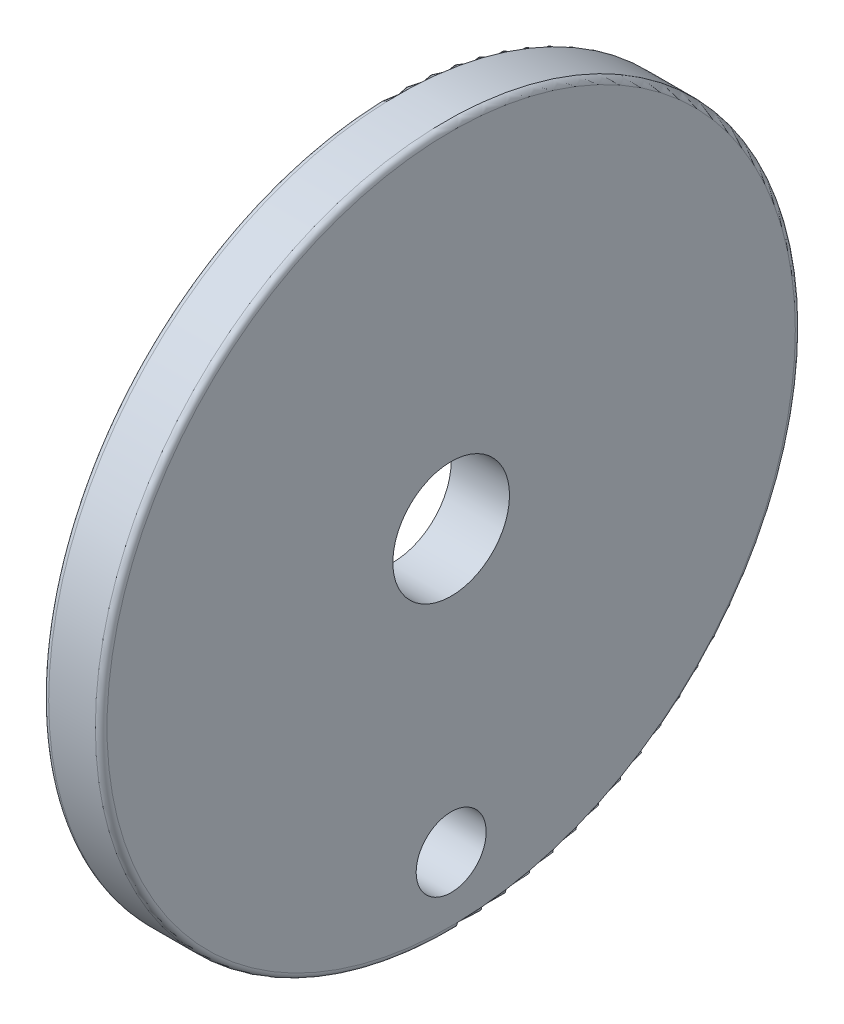
SolidWorks part; units mm, degrees
ref_plane "Přední rovina" through (0, 0, 0) normal (0, 0, 1) x (1, 0, 0)
ref_plane "Vrchní rovina" through (0, 0, 0) normal (0, 1, 0) x (1, 0, 0)
ref_plane "Pravá rovina" through (0, 0, 0) normal (1, 0, 0) x (0, 0, -1)
sketch "Skica1" plane through (0, 0, 0) normal (1, 0, 0) x (0, 0, -1)
  circle A0 centre (0, 0) radius 30
  circle A1 centre (0, 0) radius 5
  dimension "D1" = 60
  dimension "D2" = 10
extrude "Přidat vysunutím1" add sketch "Skica1" along normal blind 5
sketch "Skica2" plane through (0, 0, 0) normal (-1, 0, 0) x (0, 0, 1)
  circle A0 centre (0, 0) radius 24 construction
  circle A1 centre (0, -24) radius 3
  dimension "D1" = 6
  dimension "D2" = 48
extrude "Odebrat vysunutím1" cut sketch "Skica2" against normal up to next
fillet "Zaoblit1" radius 0.5 2 edges at (0, 0, -30) (5, 0, -30)
